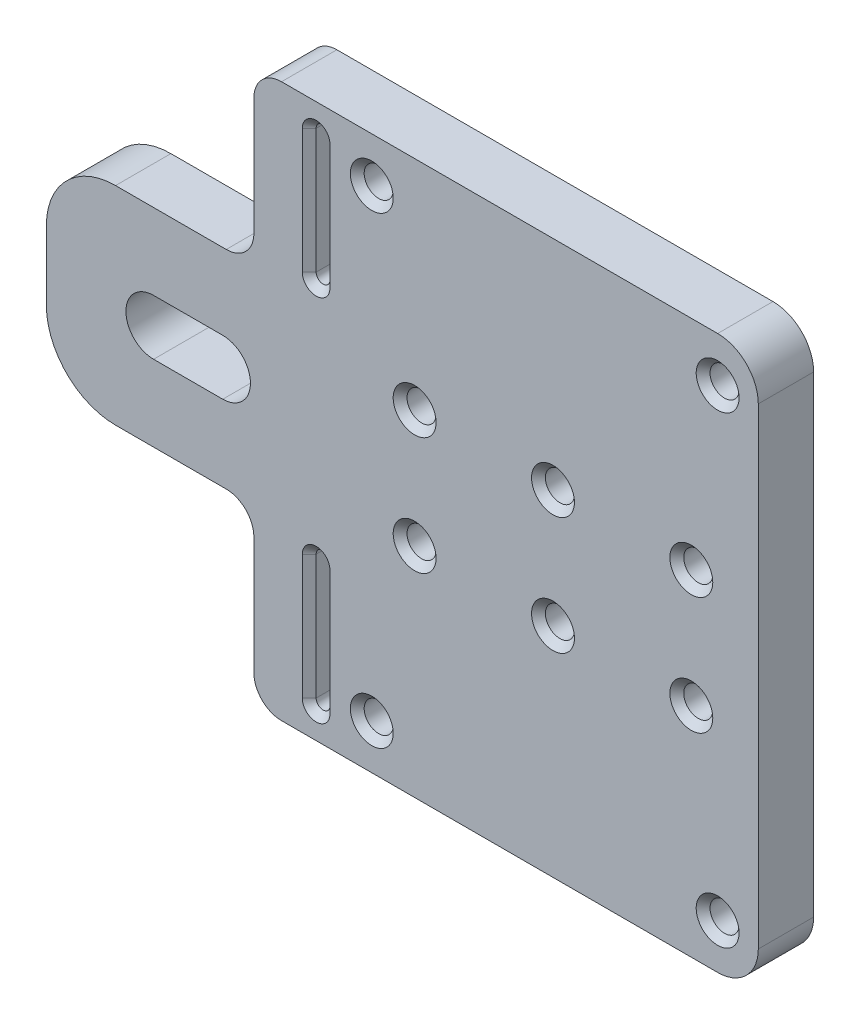
SolidWorks part; units mm, degrees
ref_plane "Plan de face" through (0, 0, 0) normal (0, 0, 1) x (1, 0, 0)
ref_plane "Plan de dessus" through (0, 0, 0) normal (0, 1, 0) x (1, 0, 0)
ref_plane "Plan de droite" through (0, 0, 0) normal (1, 0, 0) x (0, 0, -1)
sketch "Model" plane through (0, 0, 0) normal (0, 0, 1) x (1, 0, 0)
  line L0 (-24.1924, -96.5526) -> (-24.1924, -106.5526)
  line L1 (5.8076, -120.5526) -> (5.8076, -137.5526)
  line L2 (5.8076, -82.5526) -> (5.8076, -65.5526)
  line L3 (-14.1924, -116.5526) -> (1.8076, -116.5526)
  line L4 (-14.1924, -86.5526) -> (1.8076, -86.5526)
  line L5 (15.8076, -137.2146) -> (15.8076, -119.2146)
  line L6 (15.8076, -65.8906) -> (15.8076, -83.8906)
  line L7 (13.8076, -137.2146) -> (13.8076, -119.2146)
  line L8 (13.8076, -65.8906) -> (13.8076, -83.8906)
  line L9 (9.8076, -61.5526) -> (72.8534, -61.5526)
  line L10 (9.8076, -141.5526) -> (72.8534, -141.5526)
  line L11 (-8.6924, -97.5526) -> (1.3076, -97.5526)
  line L12 (1.3076, -105.5526) -> (-8.6924, -105.5526)
  line L13 (78.7284, -67.4276) -> (78.7284, -135.6776)
  line L14 (-8.6924, -101.5526) -> (104.2517, -101.5526) construction
  arc A0 (-8.6924, -97.5526) -> (-8.6924, -105.5526) centre (-8.6924, -101.5526) ccw
  arc A1 (1.3076, -105.5526) -> (1.3076, -97.5526) centre (1.3076, -101.5526) ccw
  circle A2 centre (22.8534, -68.0526) radius 2.1
  circle A3 centre (72.8534, -68.0526) radius 2.1
  circle A4 centre (29.0485, -93.0526) radius 2.1
  circle A5 centre (29.0485, -110.0526) radius 2.1
  circle A6 centre (49.0485, -93.0526) radius 2.1
  circle A7 centre (49.0485, -110.0526) radius 2.1
  circle A8 centre (69.0485, -93.0526) radius 2.1
  circle A9 centre (69.0485, -110.0526) radius 2.1
  circle A10 centre (22.8534, -135.0526) radius 2.1
  circle A11 centre (72.8534, -135.0526) radius 2.1
  arc A12 (1.8076, -86.5526) -> (5.8076, -82.5526) centre (1.8076, -82.5526) ccw
  arc A13 (5.8076, -120.5526) -> (1.8076, -116.5526) centre (1.8076, -120.5526) ccw
  arc A14 (9.8076, -61.5526) -> (5.8076, -65.5526) centre (9.8076, -65.5526) ccw
  arc A15 (5.8076, -137.5526) -> (9.8076, -141.5526) centre (9.8076, -137.5526) ccw
  arc A20 (-14.1924, -86.5526) -> (-24.1924, -96.5526) centre (-14.1924, -96.5526) ccw
  arc A21 (-24.1924, -106.5526) -> (-14.1924, -116.5526) centre (-14.1924, -106.5526) ccw
  arc A22 (78.7284, -67.4276) -> (72.8534, -61.5526) centre (72.8534, -67.4276) ccw
  arc A23 (72.8534, -141.5526) -> (78.7284, -135.6776) centre (72.8534, -135.6776) ccw
  arc A24 (15.8076, -65.8906) -> (13.8076, -65.8906) centre (14.8076, -65.8906) ccw
  arc A25 (13.8076, -83.8906) -> (15.8076, -83.8906) centre (14.8076, -83.8906) ccw
  arc A26 (15.8076, -119.2146) -> (13.8076, -119.2146) centre (14.8076, -119.2146) ccw
  arc A27 (13.8076, -137.2146) -> (15.8076, -137.2146) centre (14.8076, -137.2146) ccw
extrude "Boss.-Extru.1" add sketch "Model" along normal blind 8
chamfer "Chanfrein1" distance 1 angle 45 26 edges at (15.8076, -74.8906, 0) (14.8076, -64.8906, 0) (14.8076, -84.8906, 0) (13.8076, -74.8906, 0) (15.8076, -128.2146, 8) (14.8076, -118.2146, 8) (14.8076, -138.2146, 8) (13.8076, -128.2146, 8) (15.8076, -128.2146, 0) (14.8076, -118.2146, 0) (14.8076, -138.2146, 0) (13.8076, -128.2146, 0) (15.8076, -74.8906, 8) (14.8076, -64.8906, 8) (14.8076, -84.8906, 8) (13.8076, -74.8906, 8) (71.1485, -110.0526, 8) (51.1485, -110.0526, 8) (31.1485, -110.0526, 8) (31.1485, -93.0526, 8) (51.1485, -93.0526, 8) (71.1485, -93.0526, 8) (24.9534, -135.0526, 8) (74.9534, -135.0526, 8) (74.9534, -68.0526, 8) (24.9534, -68.0526, 8)
